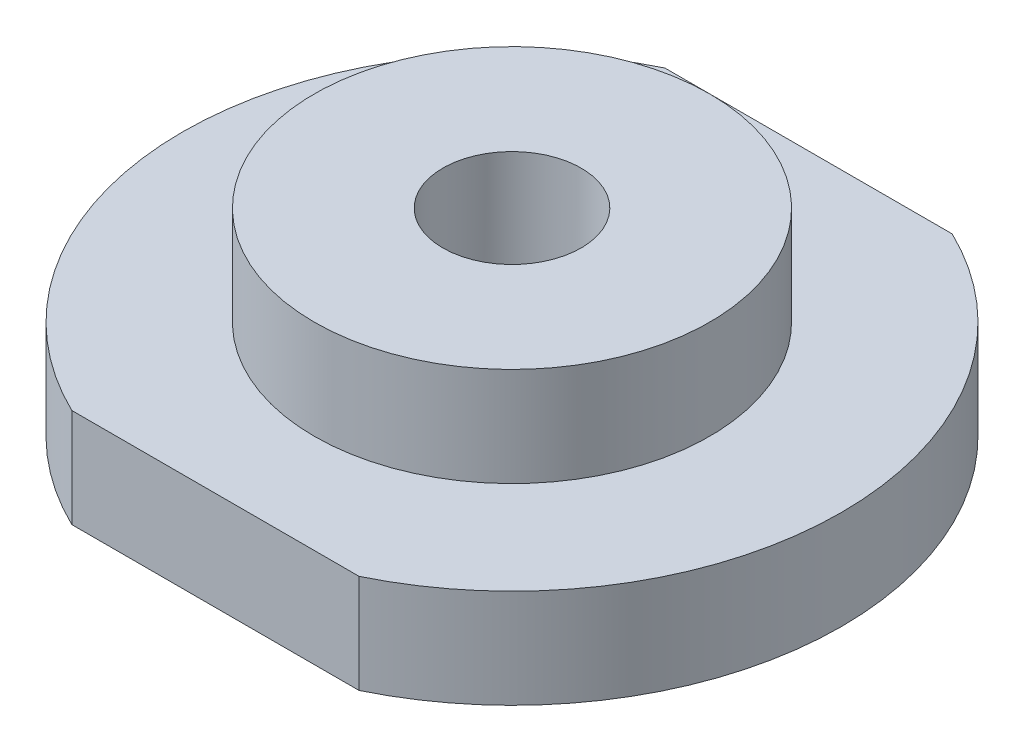
SolidWorks part; units mm, degrees
ref_plane "Front Plane" through (0, 0, 0) normal (0, 0, 1) x (1, 0, 0)
ref_plane "Top Plane" through (0, 0, 0) normal (0, 1, 0) x (1, 0, 0)
ref_plane "Right Plane" through (0, 0, 0) normal (1, 0, 0) x (0, 0, -1)
sketch "Sketch1" plane through (0, 0, 0) normal (0, 1, 0) x (1, 0, 0)
  circle A0 centre (0, 0) radius 10
  dimension "D1" = 20
extrude "Boss-Extrude2" add sketch "Sketch1" along normal blind 8
sketch "Sketch3" plane through (0, 8, 0) normal (0, 1, 0) x (1, 0, 0)
  circle A0 centre (0, 0) radius 10
  circle A1 centre (0, 0) radius 6
  dimension "D1" = 12
extrude "Cut-Extrude1" cut sketch "Sketch3" against normal blind 5
sketch "Sketch4" plane through (0, 8, 0) normal (0, 1, 0) x (1, 0, 0)
  circle A0 centre (0, 0) radius 2.1
  dimension "D1" = 4.2
extrude "Cut-Extrude2" cut sketch "Sketch4" against normal blind 11
sketch "Sketch5" plane through (0, 0, 0) normal (0, -1, 0) x (1, 0, 0)
  circle A0 centre (0, 0) radius 6
  dimension "D1" = 12
extrude "Cut-Extrude3" cut sketch "Sketch5" against normal blind 1.5
sketch "Sketch6" plane through (0, 0, 0) normal (0, -1, 0) x (1, 0, 0)
  circle A0 centre (0, 0) radius 6.5
  dimension "D1" = 13
extrude "Cut-Extrude4" cut sketch "Sketch6" against normal blind 2
sketch "Sketch7" plane through (0, 8, 0) normal (0, 1, 0) x (1, 0, 0)
  circle A0 centre (0, 0) radius 6
extrude "Cut-Extrude5" cut sketch "Sketch7" against normal blind 1
sketch "Sketch8" plane through (0, 7, 0) normal (0, 1, 0) x (1, 0, 0)
  circle A0 centre (0, 0) radius 6
extrude "Cut-Extrude6" cut sketch "Sketch8" against normal blind 1
sketch "Sketch9" plane through (0, 2, 0) normal (0, -1, 0) x (1, 0, 0)
  line L0 (0, 2.1) -> (0, 4.1) construction
  line L1 (-3.6, -2.1) -> (3.6, -2.1)
  line L2 (-3.6, -2.1) -> (-3.6, 2.1)
  line L3 (-3.6, 2.1) -> (3.6, 2.1)
  line L4 (3.6, -2.1) -> (3.6, 2.1)
  line L5 (-3.6, -2.1) -> (3.6, 2.1) construction
  line L6 (-3.6, 2.1) -> (3.6, -2.1) construction
  line L7 (-3.6, 2.1) -> (0, 4.1)
  line L8 (0, 4.1) -> (3.6, 2.1)
  line L9 (-3.6, 0) -> (3.6, 0) construction
  line L10 (0, -4.1) -> (3.6, -2.1)
  line L11 (-3.6, -2.1) -> (0, -4.1)
  circle A0 centre (0, 0) radius 6.5
  point P0 (0, 0)
  circle M9 centre (0, 0) radius 6.5
  dimension "D1" = 7.2
  dimension "D2" = 4.2
  dimension "D3" = 2
extrude "Boss-Extrude3" add sketch "Sketch9" along normal up to surface (2 mm away) contours L11 L2 L7 L8 L4 L10 M9 up to face at (0, 0, -6.5)
sketch "Sketch10" plane through (0, 0, 0) normal (0, -1, 0) x (-1, 0, 0)
  line L0 (4.3589, -9) -> (-4.3589, -9)
  line L1 (0, -10) -> (0, -9) construction
  line L2 (10, 0) -> (-10, 0) construction
  line L3 (4.3589, 9) -> (-4.3589, 9)
  circle A0 centre (0, 0) radius 10
  circle M4 centre (0, 0) radius 10
  dimension "D1" = 1
extrude "Cut-Extrude7" cut sketch "Sketch10" against normal blind 10 contours L0 M4 | L3 M4
